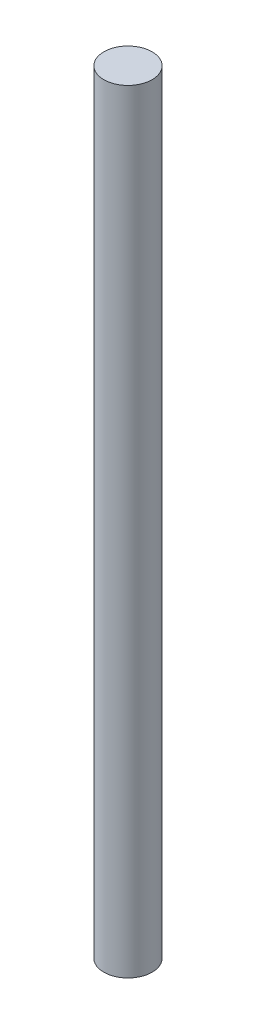
SolidWorks part; units mm, degrees
ref_plane "Front Plane" through (0, 0, 0) normal (0, 0, 1) x (1, 0, 0)
ref_plane "Top Plane" through (0, 0, 0) normal (0, 1, 0) x (1, 0, 0)
ref_plane "Right Plane" through (0, 0, 0) normal (1, 0, 0) x (0, 0, -1)
sketch "Sketch1" plane through (0, 0, 0) normal (0, 1, 0) x (1, 0, 0)
  circle A0 centre (0, 0) radius 1.5875
  dimension "D1" = 3.175
extrude "Boss-Extrude1" add sketch "Sketch1" along normal blind 50.8
